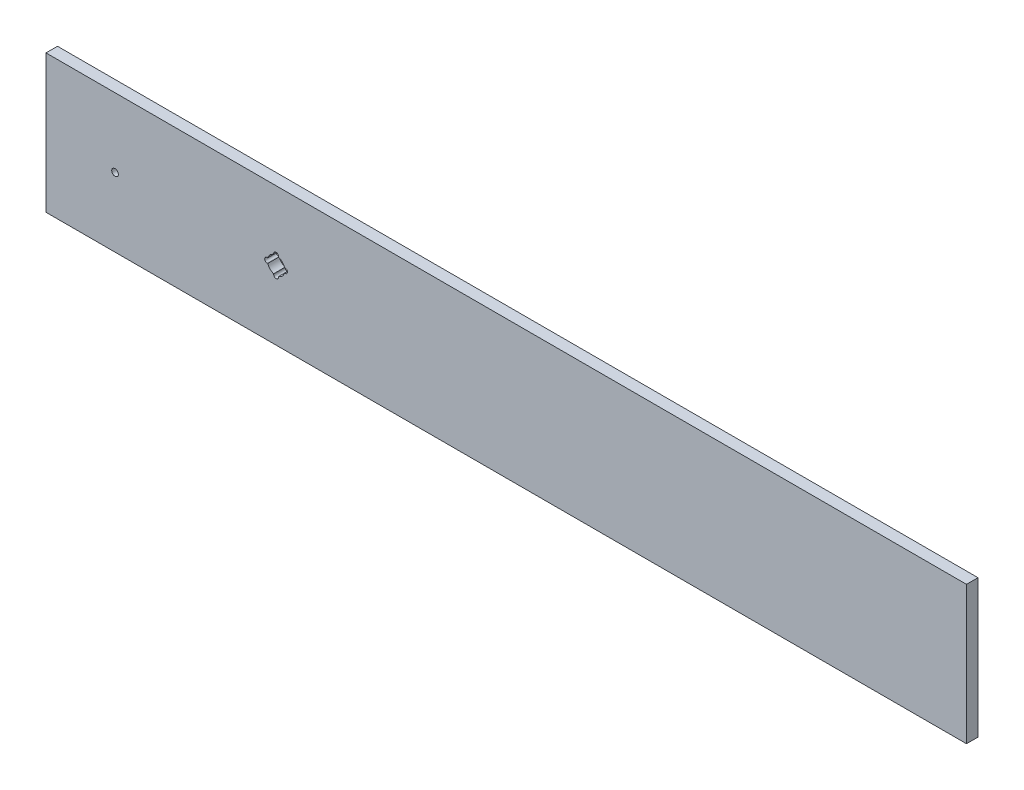
SolidWorks part; units mm, degrees
ref_plane "Front" through (0, 0, 0) normal (0, 0, 1) x (1, 0, 0)
ref_plane "Top" through (0, 0, 0) normal (0, 1, 0) x (1, 0, 0)
ref_plane "Right" through (0, 0, 0) normal (1, 0, 0) x (0, 0, -1)
sketch "Sketch1" plane through (0, 0, 0) normal (0, 0, 1) x (1, 0, 0)
  line L1 (0, 0) -> (508, 0)
  line L2 (0, 0) -> (0, 76.2)
  line L3 (0, 76.2) -> (508, 76.2)
  line L4 (508, 0) -> (508, 76.2)
  dimension "D1" = 508
  dimension "D2" = 76.2
extrude "Boss-Extrude1" add sketch "Sketch1" along normal blind 6.35
sketch "Sketch2" plane through (0, 0, 6.35) normal (0, 0, 1) x (1, 0, 0)
  line L0 (127, 76.2) -> (127, 0)
  line L3 (0, 38.1) -> (508, 38.1) construction
  line L4 (0, 76.2) -> (0, 0) construction
  line L5 (508, 0) -> (508, 76.2) construction
  line L6 (127, 43.053) -> (127, 33.147) construction
  line L7 (128.3462, 43.053) -> (128.3462, 33.147)
  line L8 (125.6538, 43.053) -> (125.6538, 33.147)
  line L9 (122.047, 38.1) -> (131.953, 38.1) construction
  line L10 (122.047, 39.4462) -> (131.953, 39.4462)
  line L11 (122.047, 36.7538) -> (131.953, 36.7538)
  line L12 (508, 76.2) -> (0, 76.2) construction
  line L13 (0, 0) -> (508, 0) construction
  arc A0 (122.392, 39.4462) -> (125.6538, 42.708) centre (127, 38.1) cw
  arc A1 (128.3462, 43.053) -> (125.6538, 43.053) centre (127, 43.053) ccw
  arc A2 (125.6538, 33.147) -> (128.3462, 33.147) centre (127, 33.147) ccw
  arc A3 (122.047, 39.4462) -> (122.047, 36.7538) centre (122.047, 38.1) ccw
  arc A4 (131.953, 36.7538) -> (131.953, 39.4462) centre (131.953, 38.1) ccw
  arc A5 (131.608, 36.7538) -> (128.3462, 33.492) centre (127, 38.1) cw
  arc A6 (131.608, 39.4462) -> (128.3462, 42.708) centre (127, 38.1) ccw
  arc A7 (122.392, 36.7538) -> (125.6538, 33.492) centre (127, 38.1) ccw
  point P16 (127, 38.1)
  point P23 (127, 38.1)
  point P29 (77.3125, 19.1057)
  dimension "D1" = 4.953
  dimension "D3" = 1.3462
  dimension "D4" = 5.1327
  dimension "D6" = 1.3462
  dimension "D7" = 4.8006
  dimension "D2" = 9.906
  dimension "D5" = 9.906
  dimension "D8" = 127
extrude "Cut-Extrude3" cut sketch "Sketch2" against normal through all contours A0 L10 L8 | L10 A6 L7 | L10 A3 L11 L8 | L11 A4 L10 L7 | A5 L11 L7 | L11 A7 L8
sketch "Sketch3" plane through (0, 0, 6.35) normal (0, 0, 1) x (1, 0, 0)
  line L0 (508, 76.2) -> (0, 76.2) construction
  line L1 (0, 76.2) -> (0, 0) construction
  circle A0 centre (38.1, 38.1) radius 1.8415
  dimension "D1" = 3.683
  dimension "D2" = 38.1
  dimension "D3" = 38.1
extrude "Cut-Extrude4" cut sketch "Sketch3" against normal through all
